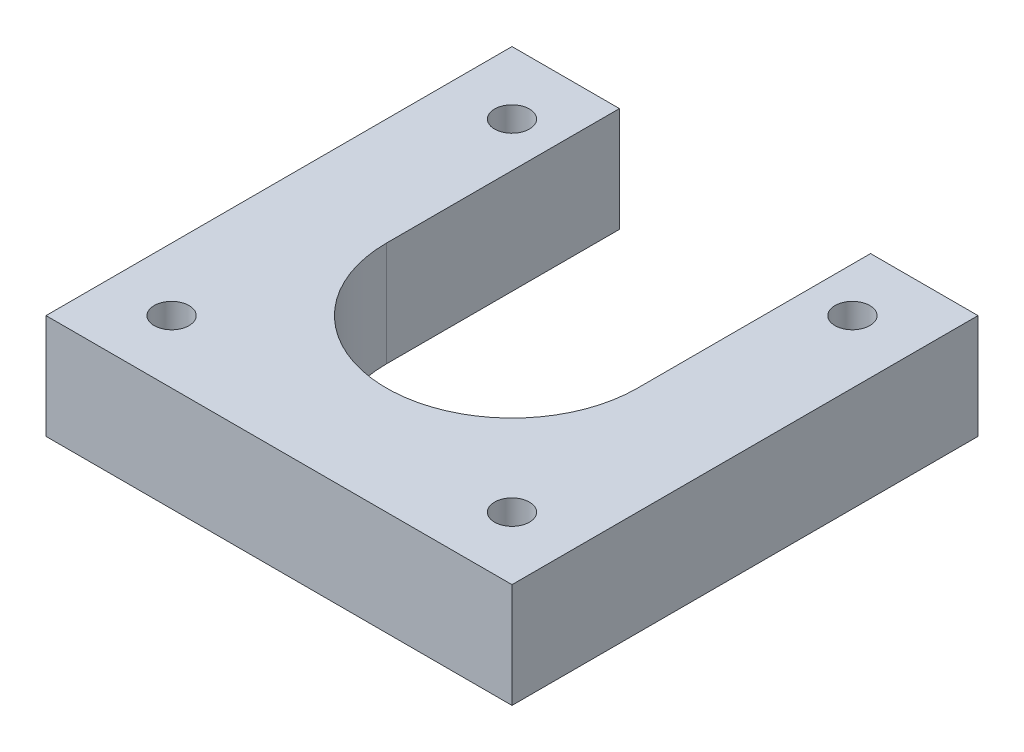
SolidWorks part; units mm, degrees
ref_plane "Front Plane" through (0, 0, 0) normal (0, 0, 1) x (1, 0, 0)
ref_plane "Top Plane" through (0, 0, 0) normal (0, 1, 0) x (1, 0, 0)
ref_plane "Right Plane" through (0, 0, 0) normal (1, 0, 0) x (0, 0, -1)
sketch "Sketch1" plane through (0, 0, 0) normal (0, 1, 0) x (1, 0, 0)
  line L0 (0, 21.209) -> (42.418, 21.209) construction
  line L1 (0, 0) -> (42.418, 0)
  line L2 (0, 0) -> (0, 42.418)
  line L4 (42.418, 0) -> (42.418, 42.418)
  line L5 (9.779, 21.209) -> (9.779, 42.418)
  line L6 (9.779, 42.418) -> (0, 42.418)
  line L7 (32.639, 21.209) -> (32.639, 42.418)
  line L8 (32.639, 42.418) -> (42.418, 42.418)
  line L10 (5.715, 36.703) -> (36.703, 36.703) construction
  line L11 (5.715, 36.703) -> (5.715, 5.715) construction
  line L12 (5.715, 5.715) -> (36.703, 5.715) construction
  line L13 (36.703, 36.703) -> (36.703, 5.715) construction
  arc A0 (9.779, 21.209) -> (32.639, 21.209) centre (21.209, 21.209) ccw
  circle A1 centre (5.715, 36.703) radius 1.5875
  circle A2 centre (36.703, 36.703) radius 1.5875
  circle A3 centre (36.703, 5.715) radius 1.5875
  circle A4 centre (5.715, 5.715) radius 1.5875
  dimension "D3" = 22.86
  dimension "D4" = 3.175
  dimension "D1" = 42.418
  dimension "D2" = 42.418
  dimension "D5" = 5.715
  dimension "D6" = 5.715
  dimension "D7" = 5.715
  dimension "D8" = 5.715
extrude "Boss-Extrude1" add sketch "Sketch1" along normal blind 9.525
